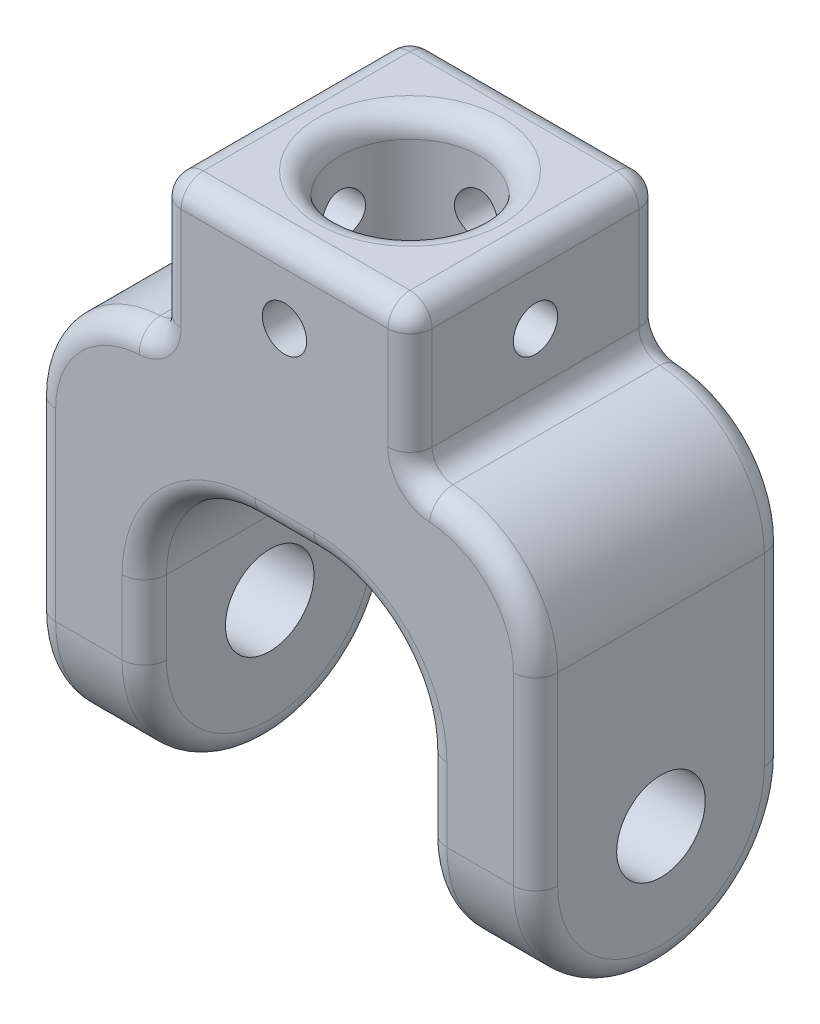
SolidWorks part; units mm, degrees
ref_plane "Ön Düzlem" through (0, 0, 0) normal (0, 0, 1) x (1, 0, 0)
ref_plane "Üst Düzlem" through (0, 0, 0) normal (0, 1, 0) x (1, 0, 0)
ref_plane "Sağ Düzlem" through (0, 0, 0) normal (1, 0, 0) x (0, 0, -1)
sketch "Çizim1" plane through (0, 0, 0) normal (0, 0, 1) x (1, 0, 0)
  line L0 (0, 0) -> (0, -42) construction
  line L1 (0, -42) -> (-19, -42) construction
  line L2 (-19, -42) -> (-34, -42)
  line L3 (-34, -42) -> (-34, 0)
  line L4 (-34, -25.5) -> (-19, -25.5) construction
  line L5 (-19, -42) -> (-19, -15)
  line L6 (-4, 0) -> (4, 0)
  line L7 (34, -42) -> (34, 0)
  line L8 (19, -42) -> (34, -42)
  line L9 (19, -42) -> (19, -15)
  line L10 (17, 14.8661) -> (17, 34.8661)
  line L12 (-17, 14.8661) -> (-17, 34.8661)
  line L13 (-17, 34.8661) -> (17, 34.8661)
  line L14 (0, 0) -> (-34, 0) construction
  arc A0 (-4, 0) -> (-19, -15) centre (-4, -15) ccw
  arc A1 (4, 0) -> (19, -15) centre (4, -15) cw
  arc A2 (-34, 0) -> (-17, 14.8661) centre (-19, 0) cw
  arc A3 (34, 0) -> (17, 14.8661) centre (19, 0) ccw
  point P24 (0, 34.8661)
  dimension "D6" = 15
  dimension "D10" = 15
  dimension "D1" = 19
  dimension "D2" = 15
  dimension "D3" = 42
  dimension "D4" = 42
  dimension "D5" = 16.5
  dimension "D7" = 17
  dimension "D9" = 20
extrude "Yükseklik-Ekstrüzyon2" add sketch "Çizim1" along normal mid plane 34
sketch "Çizim2" plane through (0, 34.8661, 0) normal (0, 1, 0) x (1, 0, 0)
  circle A0 centre (0, 0) radius 9.5
  dimension "D1" = 19
extrude "Kes-Ekstrüzyon1" cut sketch "Çizim2" against normal through all
sketch "Çizim3" plane through (-34, 0, 0) normal (-1, 0, 0) x (0, 0, 1)
  line L0 (0, -42) -> (0, -25) construction
  line L5 (17, -42) -> (-17, -42) construction
  line L6 (17, -25) -> (-17, -25) construction
  line L7 (17, 0) -> (17, -42) construction
  line L8 (-17, 0) -> (-17, -42) construction
  line L9 (17, 0) -> (17, -42)
  line L10 (17, -42) -> (-17, -42)
  line L11 (-17, 0) -> (-17, -42)
  circle A0 centre (0, -25) radius 17
  point P9 (0, -25)
  line M2 (-17, -42) -> (17, -42)
  line M3 (17, -42) -> (17, 0)
  dimension "D1" = 17
  dimension "D2" = 34
extrude "Kes-Ekstrüzyon2" cut sketch "Çizim3" against normal through all contours A0 L11 M2 | A0 L10 M3
sketch "Çizim4" plane through (-34, 0, 0) normal (-1, 0, 0) x (0, 0, 1)
  circle A0 centre (0, -25) radius 6
  dimension "D1" = 12
extrude "Kes-Ekstrüzyon3" cut sketch "Çizim4" against normal through all
sketch "Çizim5" plane through (17, 0, 0) normal (1, 0, 0) x (0, 0, -1)
  line L0 (0, 34.8661) -> (0, 24.8661) construction
  line L1 (-17, 34.8661) -> (17, 34.8661) construction
  circle A0 centre (0, 24.8661) radius 3
  dimension "D2" = 6
  dimension "D1" = 10
extrude "Kes-Ekstrüzyon4" cut sketch "Çizim5" against normal through all
sketch "Çizim6" plane through (0, 0, 17) normal (0, 0, 1) x (1, 0, 0)
  line L0 (0, 34.8661) -> (0, 24.8661) construction
  line L1 (17, 34.8661) -> (-17, 34.8661) construction
  circle A0 centre (0, 24.8661) radius 3
  dimension "D2" = 6
  dimension "D1" = 10
extrude "Kes-Ekstrüzyon5" cut sketch "Çizim6" against normal through all
fillet "Radyus1" radius 3 33 edges at (17, 24.8661, -17) (-28.8742, 11.2916, 17) (-28.8742, 11.2916, -17) (-34, -12.5, -17) (-34, -42, 0) (0, 0, 17) (-14.6066, -4.3934, 17) (-19, -20, 17) (-19, -42, 0) (-19, -20, -17) (-14.6066, -4.3934, -17) (0, 0, -17) (14.6066, -4.3934, -17) (19, -20, -17) (19, -42, 0) (19, -20, 17) (28.8742, 11.2916, -17) (34, -12.5, -17) (34, -42, 0) (34, -12.5, 17) (-9.5, 34.8661, 0) (-17, 14.8661, 0) (-17, 34.8661, 0) (-17, 24.8661, -17) (0, 34.8661, -17) (17, 14.8661, 0) (17, 34.8661, 0) (17, 24.8661, 17) (0, 34.8661, 17) (-17, 24.8661, 17) (-34, -12.5, 17) (14.6066, -4.3934, 17) (28.8742, 11.2916, 17)
